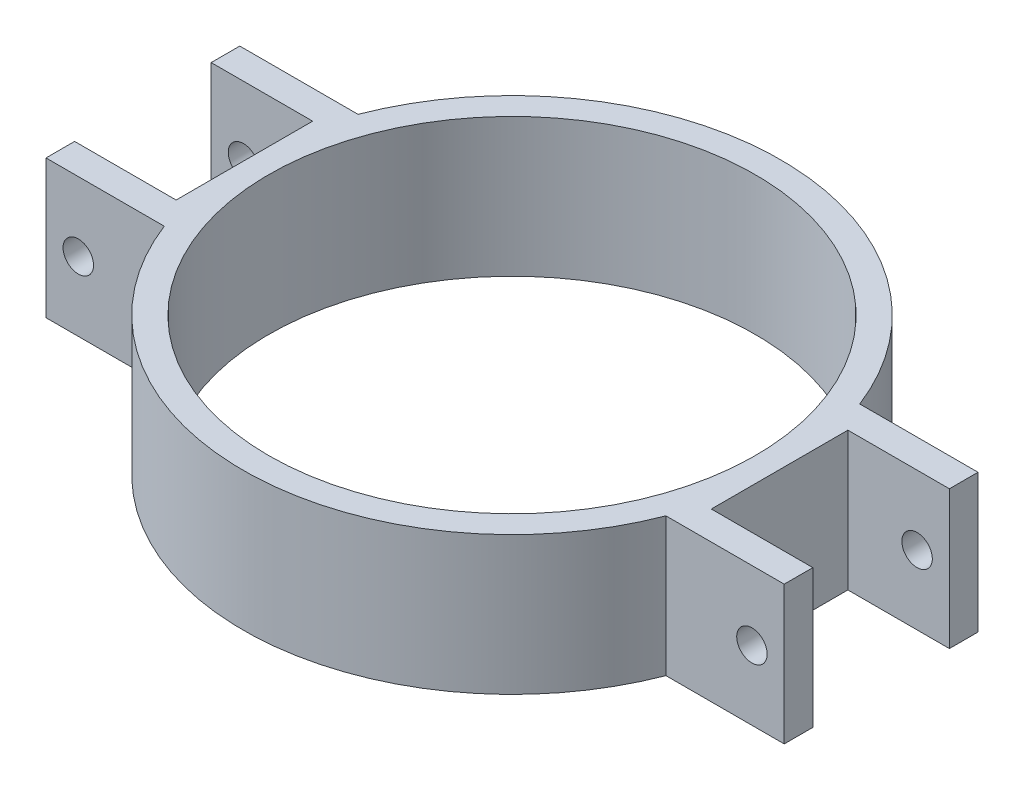
SolidWorks part; units mm, degrees
ref_plane "前视基准面" through (0, 0, 0) normal (0, 0, 1) x (1, 0, 0)
ref_plane "上视基准面" through (0, 0, 0) normal (0, 1, 0) x (1, 0, 0)
ref_plane "右视基准面" through (0, 0, 0) normal (1, 0, 0) x (0, 0, -1)
sketch "草图1" plane through (0, 0, 0) normal (0, 1, 0) x (1, 0, 0)
  line L0 (-40, 7.4) -> (-29, 7.4)
  line L1 (-27.1825, -10.5) -> (-40, -10.5)
  line L2 (-29, 7.4) -> (-29, -7.4)
  line L3 (-27.1825, 10.5) -> (-40, 10.5)
  line L4 (-40, -10.5) -> (-40, -7.4)
  line L5 (-29, -7.4) -> (-40, -7.4)
  line L6 (-40, 7.4) -> (-40, 10.5)
  line L7 (27.1825, 10.5) -> (40, 10.5)
  line L8 (40, 10.5) -> (40, 7.4)
  line L9 (40, -10.5) -> (27.1825, -10.5)
  line L10 (40, -7.4) -> (40, -10.5)
  line L11 (40, 7.4) -> (29, 7.4)
  line L12 (29, 7.4) -> (29, -7.4)
  line L13 (29, -7.4) -> (40, -7.4)
  circle A0 centre (0, 0) radius 26.37
  arc A2 (-27.1825, -10.5) -> (27.1825, -10.5) centre (0, 0) ccw
  arc A3 (27.1825, 10.5) -> (-27.1825, 10.5) centre (0, 0) ccw
extrude "凸台-拉伸1" add sketch "草图1" along normal blind 15
sketch "草图2" plane through (0, 0, -10.5) normal (0, 0, -1) x (-1, 0, 0)
  circle A0 centre (36.5, 7.5) radius 1.65
  circle A1 centre (-36.5, 7.5) radius 1.65
extrude "切除-拉伸1" cut sketch "草图2" against normal blind 23
